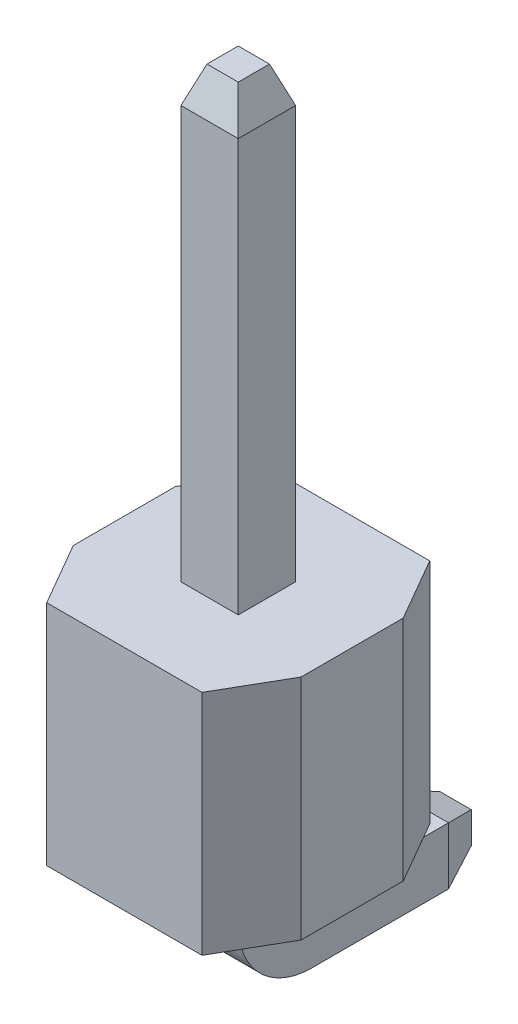
SolidWorks part; units mm, degrees
ref_plane "Front Plane" through (0, 0, 0) normal (0, 0, 1) x (1, 0, 0)
ref_plane "Top Plane" through (0, 0, 0) normal (0, 1, 0) x (1, 0, 0)
ref_plane "Right Plane" through (0, 0, 0) normal (1, 0, 0) x (0, 0, -1)
sketch "Sketch1" plane through (0, 0, 0) normal (1, 0, 0) x (0, 0, -1)
  line L0 (-2.4243, 3.1405) -> (-2.4243, -4.8595)
  line L1 (-1.9243, -5.3595) -> (0.1157, -5.3595)
  arc A0 (-2.4243, -4.8595) -> (-1.9243, -5.3595) centre (-1.9243, -4.8595) ccw
  point P5 (-2.4243, -5.3595)
  dimension "D3" = 0.5
  dimension "D1" = 8.5
  dimension "D2" = 2.54
sketch "Sketch2" plane through (0, 0, 0) normal (0, 0, 1) x (1, 0, 0)
  line L1 (0.32, -5.0395) -> (-0.32, -5.0395)
  line L2 (0.32, -5.0395) -> (0.32, -5.6795)
  line L3 (0.32, -5.6795) -> (-0.32, -5.6795)
  line L4 (-0.32, -5.0395) -> (-0.32, -5.6795)
  line L5 (0.32, -5.0395) -> (-0.32, -5.6795) construction
  line L6 (0.32, -5.6795) -> (-0.32, -5.0395) construction
  point P0 (0, -5.3595)
  dimension "D1" = 0.64
  dimension "D2" = 0.64
sweep "Sweep1" add profiles "Sketch2" path "Sketch1"
chamfer "Chamfer1" distance 0.4 angle 20 8 edges at (0, -5.6795, 0) (-0.32, -5.3595, 0) (0.32, -5.3595, 0) (0, -5.0395, 0) (0, 3.1405, 2.1043) (-0.32, 3.1405, 2.4243) (0.32, 3.1405, 2.4243) (0, 3.1405, 2.7443)
ref_plane "Plane1" through (0, -4.3995, 0) normal (0, 1, 0) x (-1, 0, 0)
sketch "Sketch5" plane through (0, -4.3995, 0) normal (0, 1, 0) x (-1, 0, 0)
  line L0 (0.1744, 2.2498) -> (-0.1744, 2.5987) construction
  line L1 (-0.1744, 2.5987) -> (0.1744, 2.5987) construction
  line L2 (0.1744, 2.5987) -> (-0.1744, 2.2498) construction
sketch "Sketch6" plane through (0, -4.3995, 0) normal (0, 1, 0) x (-1, 0, 0)
  line L0 (0.1744, 2.2498) -> (-0.1744, 2.5987) construction
  line L1 (-1.27, 1.1543) -> (1.27, 1.1543)
  line L2 (-1.27, 1.1543) -> (-1.27, 3.6943)
  line L3 (-1.27, 3.6943) -> (1.27, 3.6943)
  line L4 (1.27, 1.1543) -> (1.27, 3.6943)
  line L5 (-1.27, 1.1543) -> (1.27, 3.6943) construction
  line L6 (-1.27, 3.6943) -> (1.27, 1.1543) construction
  point P0 (0, 2.4243)
  dimension "D1" = 2.54
  dimension "D2" = 2.54
extrude "Extrude1" add sketch "Sketch6" along normal blind 2.54 separate body
chamfer "Chamfer2" distance 0.7 angle 30 4 edges at (-1.27, -3.1295, 3.6943) (-1.27, -3.1295, 1.1543) (1.27, -3.1295, 3.6943) (1.27, -3.1295, 1.1543)
